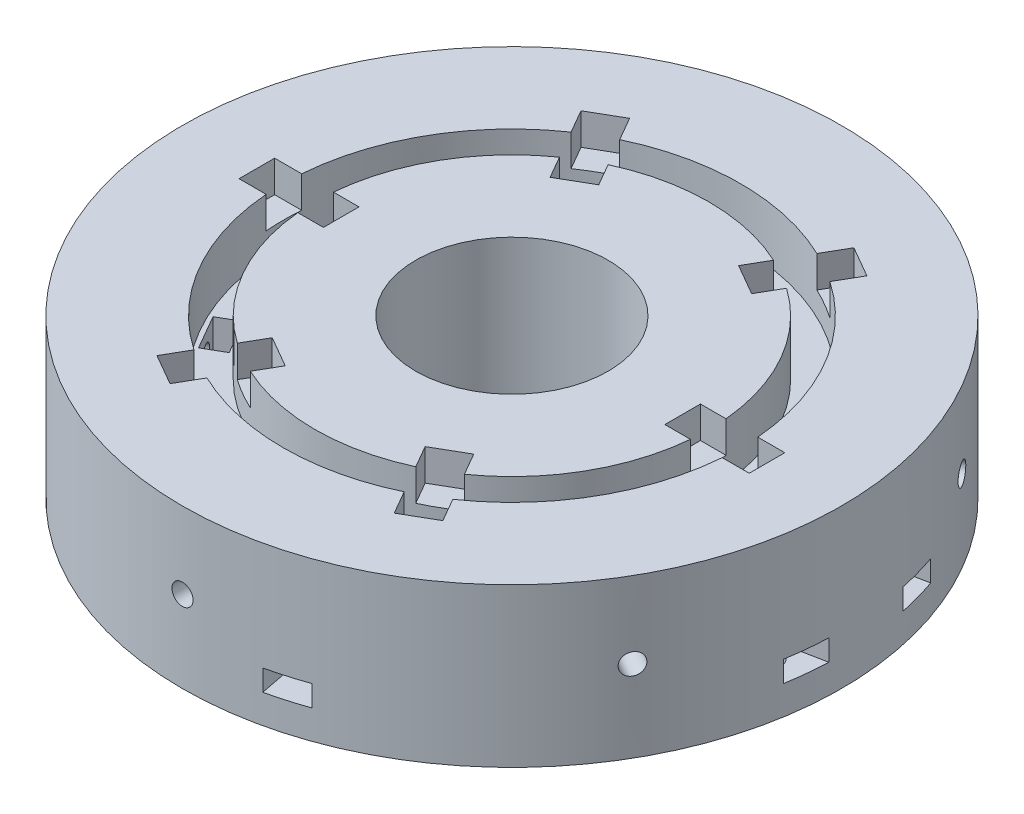
SolidWorks part; units mm, degrees
ref_plane "Front Plane" through (0, 0, 0) normal (0, 0, 1) x (1, 0, 0)
ref_plane "Top Plane" through (0, 0, 0) normal (0, 1, 0) x (1, 0, 0)
ref_plane "Right Plane" through (0, 0, 0) normal (1, 0, 0) x (0, 0, -1)
sketch "Sketch1" plane through (0, 0, 0) normal (0, 1, 0) x (1, 0, 0)
  circle A0 centre (0, 0) radius 62.5
  circle A1 centre (0, 0) radius 18.25
  dimension "D1" = 125
  dimension "D2" = 36.5
extrude "Boss-Extrude1" add sketch "Sketch1" along normal blind 30 contours A0
sketch "Sketch2" plane through (0, 30, 0) normal (0, 1, 0) x (1, 0, 0)
  line L0 (18.25, 0) -> (62.5, 0) construction
  line L1 (40.375, 0) -> (40.375, 3.4672) construction
  line L2 (32.375, 3.375) -> (48.375, 3.375)
  line L3 (32.375, 3.375) -> (32.375, -3.375)
  line L4 (32.375, -3.375) -> (48.375, -3.375)
  line L5 (48.375, 3.375) -> (48.375, -3.375)
  line L6 (19.1103, -26.3501) -> (13.2647, -29.7251)
  line L7 (19.1103, -26.3501) -> (27.1103, -40.2065)
  line L8 (27.1103, -40.2065) -> (21.2647, -43.5815)
  line L9 (13.2647, -29.7251) -> (21.2647, -43.5815)
  line L10 (-13.2647, -29.7251) -> (-19.1103, -26.3501)
  line L11 (-13.2647, -29.7251) -> (-21.2647, -43.5815)
  line L12 (-21.2647, -43.5815) -> (-27.1103, -40.2065)
  line L13 (-19.1103, -26.3501) -> (-27.1103, -40.2065)
  line L14 (-32.375, -3.375) -> (-32.375, 3.375)
  line L15 (-32.375, -3.375) -> (-48.375, -3.375)
  line L16 (-48.375, -3.375) -> (-48.375, 3.375)
  line L17 (-32.375, 3.375) -> (-48.375, 3.375)
  line L18 (-19.1103, 26.3501) -> (-13.2647, 29.7251)
  line L19 (-19.1103, 26.3501) -> (-27.1103, 40.2065)
  line L20 (-27.1103, 40.2065) -> (-21.2647, 43.5815)
  line L21 (-13.2647, 29.7251) -> (-21.2647, 43.5815)
  line L22 (13.2647, 29.7251) -> (19.1103, 26.3501)
  line L23 (13.2647, 29.7251) -> (21.2647, 43.5815)
  line L24 (21.2647, 43.5815) -> (27.1103, 40.2065)
  line L25 (19.1103, 26.3501) -> (27.1103, 40.2065)
  circle A0 centre (0, 0) radius 40.375 construction
  circle A1 centre (0, 0) radius 18.25 construction
  circle A2 centre (0, 0) radius 62.5 construction
  point P10 (40.375, 0)
  point P17 (40.375, 3.375)
  point P18 (48.375, 0)
  point P41 (0, 0)
  dimension "D1" = 16
  dimension "D2" = 6.75
  dimension "D3" = 6
extrude "Cut-Extrude2" cut sketch "Sketch2" against normal blind 6
sketch "Sketch3" plane through (0, 30, 0) normal (0, 1, 0) x (1, 0, 0)
  line L0 (18.25, 0) -> (62.5, 0) construction
  line L1 (18.25, 0) -> (62.5, 0) construction
  line L3 (38, 7.25) -> (42.75, 7.25) construction
  line L4 (38, 7.25) -> (38, -7.25) construction
  line L5 (38, -7.25) -> (42.75, -7.25) construction
  line L6 (42.75, 7.25) -> (42.75, -7.25) construction
  circle A0 centre (0, 0) radius 40.375 construction
  circle A1 centre (0, 0) radius 40.375 construction
  circle A2 centre (0, 0) radius 43.375
  circle A3 centre (0, 0) radius 37.375
  point P9 (42.75, 0)
  point P10 (40.375, 7.25)
  dimension "D1" = 14.5
  dimension "D2" = 4.75
  dimension "D3" = 3
  dimension "D4" = 3
extrude "Cut-Extrude3" cut sketch "Sketch3" against normal blind 10.5 contours A2 | A3
sketch "Sketch5" plane through (0, 19.5, 0) normal (0, 1, 0) x (1, 0, 0)
  line L0 (0, 42.5) -> (0, 43.375) construction
  line L1 (-3.75, 42.5) -> (3.75, 42.5)
  line L2 (-3.75, 42.5) -> (-3.75, 38.25)
  line L3 (-3.75, 38.25) -> (3.75, 38.25)
  line L4 (3.75, 42.5) -> (3.75, 38.25)
  line L5 (-3.75, 42.5) -> (3.75, 38.25) construction
  line L6 (-3.75, 38.25) -> (3.75, 42.5) construction
  line L7 (0, 38.25) -> (0, 37.375) construction
  line L8 (34.9311, 24.4976) -> (31.2505, 22.3726)
  line L9 (34.9311, 24.4976) -> (38.6811, 18.0024)
  line L10 (38.6811, 18.0024) -> (35.0005, 15.8774)
  line L11 (31.2505, 22.3726) -> (35.0005, 15.8774)
  line L12 (38.6811, -18.0024) -> (35.0005, -15.8774)
  line L13 (38.6811, -18.0024) -> (34.9311, -24.4976)
  line L14 (34.9311, -24.4976) -> (31.2505, -22.3726)
  line L15 (35.0005, -15.8774) -> (31.2505, -22.3726)
  line L16 (3.75, -42.5) -> (3.75, -38.25)
  line L17 (3.75, -42.5) -> (-3.75, -42.5)
  line L18 (-3.75, -42.5) -> (-3.75, -38.25)
  line L19 (3.75, -38.25) -> (-3.75, -38.25)
  line L20 (-34.9311, -24.4976) -> (-31.2505, -22.3726)
  line L21 (-34.9311, -24.4976) -> (-38.6811, -18.0024)
  line L22 (-38.6811, -18.0024) -> (-35.0005, -15.8774)
  line L23 (-31.2505, -22.3726) -> (-35.0005, -15.8774)
  line L24 (-38.6811, 18.0024) -> (-35.0005, 15.8774)
  line L25 (-38.6811, 18.0024) -> (-34.9311, 24.4976)
  line L26 (-34.9311, 24.4976) -> (-31.2505, 22.3726)
  line L27 (-35.0005, 15.8774) -> (-31.2505, 22.3726)
  circle A1 centre (0, 0) radius 43.375 construction
  circle A2 centre (0, 0) radius 37.375 construction
  point P0 (0, 40.375)
  point P37 (0, 0)
  dimension "D1" = 7.5
  dimension "D2" = 4.25
  dimension "D3" = 6
extrude "Cut-Extrude5" cut sketch "Sketch5" against normal blind 8
sketch "Sketch6" plane through (36.8061, 0, -21.25) normal (-0.866, 0, 0.5) x (0.5, 0, 0.866)
  line L0 (0, 15.5) -> (0, 19.5) construction
  line L1 (3.75, 19.5) -> (-3.75, 19.5) construction
  line L2 (0, 15.5) -> (0, 11.5) construction
  circle A0 centre (0, 15.5) radius 2
  point P7 (0, 0)
  point P8 (0, 0)
  dimension "D1" = 4
  dimension "D2" = 4
extrude "Cut-Extrude6" cut sketch "Sketch6" along direction (0.866, 0, -0.5) on the side against the normal up to surface and the other way blind 10
pattern_circular "CirPattern1" count 6 over 360 about axis through (0, 0, 0) along (0, 1, 0) of "Cut-Extrude6"
sketch "Sketch7" plane through (0, 0, 0) normal (0, -1, 0) x (1, 0, 0)
  circle A0 centre (15.7036, 51.5748) radius 2 construction
  circle A1 centre (56.5228, 7.3599) radius 2 construction
  circle A2 centre (52.0932, -15.1106) radius 2 construction
  circle A3 centre (15.7036, 51.5748) radius 2
  circle A4 centre (56.5228, 7.3599) radius 2
  circle A5 centre (52.0932, -15.1106) radius 2
extrude "Cut-Extrude7" cut sketch "Sketch7" against normal blind 9.5
sketch "Sketch8" plane through (0, 9.5, 0) normal (0, -1, 0) x (1, 0, 0)
  line L0 (56.5228, 7.3599) -> (62.1874, 6.2433) construction
  line L1 (52.0932, -15.1106) -> (60.2239, -16.7133) construction
  line L2 (15.7036, 51.5748) -> (17.3718, 60.0372) construction
  line L3 (21.0998, 50.511) -> (22.6053, 58.1483) construction
  line L4 (45.6333, -19.443) -> (56.4256, -21.5705) construction
  line L5 (12.4432, 54.4242) -> (13.734, 60.9723)
  line L6 (56.3416, -15.948) -> (54.9427, -11.8501) construction
  line L7 (54.9427, -11.8501) -> (50.6943, -11.0126)
  line L8 (50.6943, -11.0126) -> (47.8449, -14.2731)
  line L9 (47.8449, -14.2731) -> (49.2438, -18.371)
  line L10 (49.2438, -18.371) -> (53.4921, -19.2085)
  line L11 (53.4921, -19.2085) -> (56.3416, -15.948) construction
  line L12 (60.7712, 6.5224) -> (59.3723, 10.6204) construction
  line L13 (59.3723, 10.6204) -> (55.1239, 11.4578)
  line L14 (55.1239, 11.4578) -> (52.2745, 8.1974)
  line L15 (52.2745, 8.1974) -> (53.6734, 4.0995)
  line L16 (53.6734, 4.0995) -> (57.9217, 3.262)
  line L17 (57.9217, 3.262) -> (60.7712, 6.5224) construction
  line L18 (16.5411, 55.8231) -> (12.4432, 54.4242) construction
  line L19 (12.4432, 54.4242) -> (11.6057, 50.1759)
  line L20 (11.6057, 50.1759) -> (14.8661, 47.3264)
  line L21 (14.8661, 47.3264) -> (18.9641, 48.7253)
  line L22 (18.9641, 48.7253) -> (19.8016, 52.9737)
  line L23 (19.8016, 52.9737) -> (16.5411, 55.8231) construction
  line L24 (19.8016, 52.9737) -> (20.9656, 58.8786)
  line L25 (59.3723, 10.6204) -> (61.6674, 10.1679)
  line L26 (57.9217, 3.262) -> (62.4551, 2.3683)
  line L27 (54.9427, -11.8501) -> (61.1186, -13.0676)
  line L28 (53.4921, -19.2085) -> (59.1062, -20.3152)
  circle A0 centre (0, 0) radius 62.5 construction
  circle A1 centre (52.0932, -15.1106) radius 3.75 construction
  circle A2 centre (56.5228, 7.3599) radius 3.75 construction
  circle A3 centre (15.7036, 51.5748) radius 3.75 construction
  arc A4 (59.1062, -20.3152) -> (61.1186, -13.0676) centre (0, 0) ccw
  arc A5 (62.4551, 2.3683) -> (61.6674, 10.1679) centre (0, 0) ccw
  arc A6 (20.9656, 58.8786) -> (13.734, 60.9723) centre (0, 0) ccw
  point P11 (0, 0)
  point P44 (61.1968, -12.6965)
  dimension "D1" = 7.5
  dimension "D2" = 7.5
  dimension "D3" = 7.5
extrude "Cut-Extrude8" cut sketch "Sketch8" along normal blind 4
